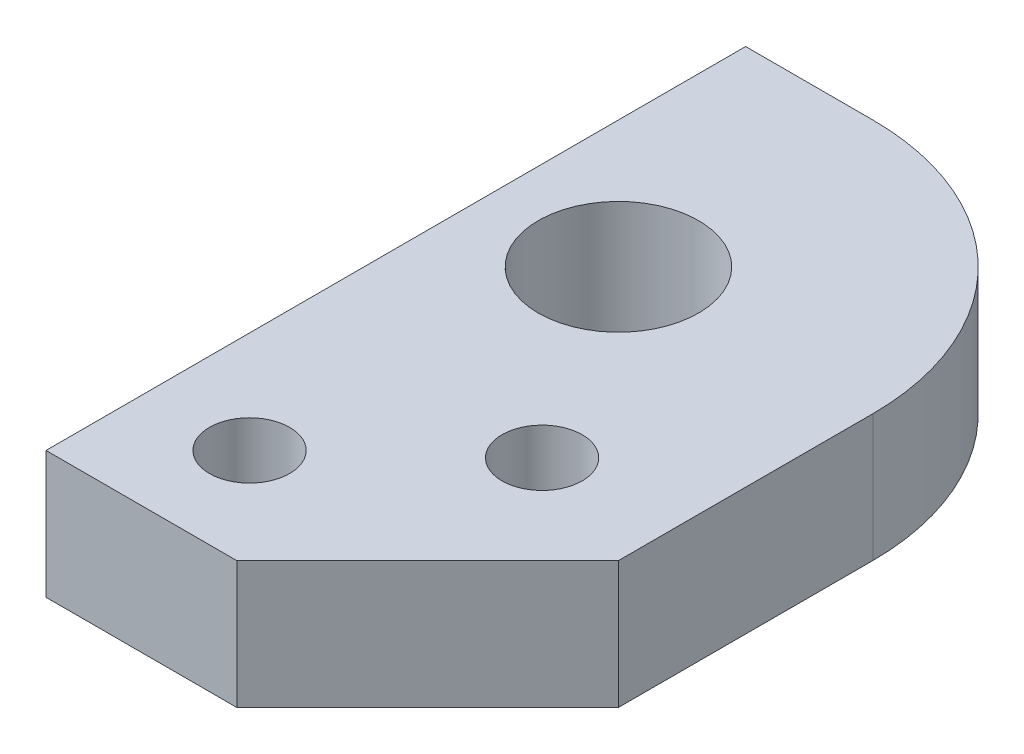
SolidWorks part; units mm, degrees
ref_plane "Front Plane" through (0, 0, 0) normal (0, 0, 1) x (1, 0, 0)
ref_plane "Top Plane" through (0, 0, 0) normal (0, 1, 0) x (1, 0, 0)
ref_plane "Right Plane" through (0, 0, 0) normal (1, 0, 0) x (0, 0, -1)
sketch "Sketch2" plane through (0, 0, 0) normal (0, 1, 0) x (1, 0, 0)
  line L3 (6.35, 127) -> (12.7, 127)
  line L5 (25.4, 101.6) -> (25.4, 114.3)
  line L11 (6.35, 127) -> (6.35, 101.6)
  line L14 (25.4, 101.6) -> (15.875, 92.075)
  line L15 (6.35, 101.6) -> (6.35, 92.075)
  line L16 (6.35, 92.075) -> (15.875, 92.075)
  circle A0 centre (11.43, 97.155) radius 2
  circle A1 centre (19.05, 104.14) radius 2
  arc A3 (12.7, 127) -> (25.4, 114.3) centre (12.7, 114.3) cw
  circle A5 centre (12.7, 114.3) radius 4.0005
  point P25 (25.4, 0)
  dimension "D6" = 10.16
  dimension "D7" = 6.35
  dimension "D5" = 12.7
  dimension "D8" = 5.08
  dimension "D3" = 4
  dimension "D4" = 4
  dimension "D12" = 8.001
  dimension "D1" = 25.4
  dimension "D2" = 19.05
  dimension "D9" = 5.08
  dimension "D10" = 9.525
  dimension "D11" = 9.525
extrude "Boss-Extrude1" add sketch "Sketch2" along normal blind 6.35
